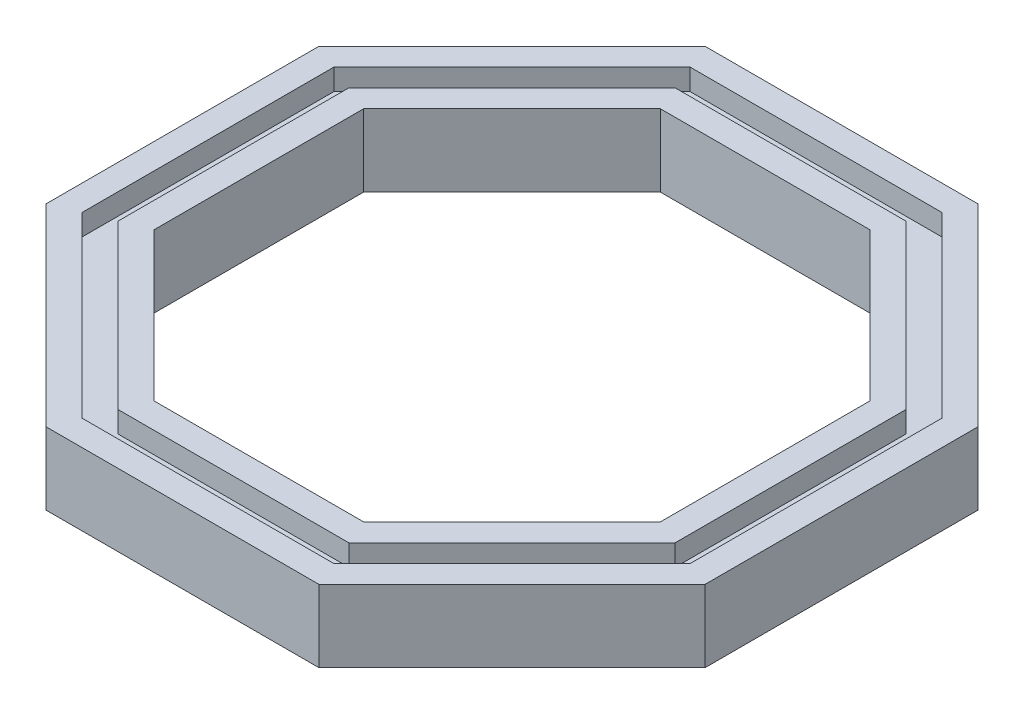
SolidWorks part; units mm, degrees
ref_plane "정면" through (0, 0, 0) normal (0, 0, 1) x (1, 0, 0)
ref_plane "윗면" through (0, 0, 0) normal (0, 1, 0) x (1, 0, 0)
ref_plane "우측면" through (0, 0, 0) normal (1, 0, 0) x (0, 0, -1)
sketch "스케치1" plane through (0, 0, 0) normal (0, 1, 0) x (1, 0, 0)
  line L0 (-55, 0) -> (55, 0) construction
  line L1 (5.9316, -14.3201) -> (14.3201, -5.9316)
  line L2 (14.3201, -5.9316) -> (14.3201, 5.9316)
  line L3 (14.3201, 5.9316) -> (5.9316, 14.3201)
  line L4 (5.9316, 14.3201) -> (-5.9316, 14.3201)
  line L5 (-5.9316, 14.3201) -> (-14.3201, 5.9316)
  line L6 (-14.3201, 5.9316) -> (-14.3201, -5.9316)
  line L7 (-14.3201, -5.9316) -> (-5.9316, -14.3201)
  line L8 (-5.9316, -14.3201) -> (5.9316, -14.3201)
  line L9 (6.4286, -15.5201) -> (15.5201, -6.4286)
  line L10 (15.5201, -6.4286) -> (15.5201, 6.4286)
  line L11 (15.5201, 6.4286) -> (6.4286, 15.5201)
  line L12 (6.4286, 15.5201) -> (-6.4286, 15.5201)
  line L13 (-6.4286, 15.5201) -> (-15.5201, 6.4286)
  line L14 (-15.5201, 6.4286) -> (-15.5201, -6.4286)
  line L15 (-15.5201, -6.4286) -> (-6.4286, -15.5201)
  line L16 (-6.4286, -15.5201) -> (6.4286, -15.5201)
  line L17 (5.4345, -13.1201) -> (13.1201, -5.4345)
  line L18 (13.1201, -5.4345) -> (13.1201, 5.4345)
  line L19 (13.1201, 5.4345) -> (5.4345, 13.1201)
  line L20 (5.4345, 13.1201) -> (-5.4345, 13.1201)
  line L21 (-5.4345, 13.1201) -> (-13.1201, 5.4345)
  line L22 (-13.1201, 5.4345) -> (-13.1201, -5.4345)
  line L23 (-13.1201, -5.4345) -> (-5.4345, -13.1201)
  line L24 (-5.4345, -13.1201) -> (5.4345, -13.1201)
  line L25 (4.9375, -11.9201) -> (11.9201, -4.9375)
  line L26 (11.9201, -4.9375) -> (11.9201, 4.9375)
  line L27 (11.9201, 4.9375) -> (4.9375, 11.9201)
  line L28 (4.9375, 11.9201) -> (-4.9375, 11.9201)
  line L29 (-4.9375, 11.9201) -> (-11.9201, 4.9375)
  line L30 (-11.9201, 4.9375) -> (-11.9201, -4.9375)
  line L31 (-11.9201, -4.9375) -> (-4.9375, -11.9201)
  line L32 (-4.9375, -11.9201) -> (4.9375, -11.9201)
  circle A0 centre (0, 0) radius 15.5 construction
  dimension "D1" = 31
  dimension "D2" = 1.2
  dimension "D3" = 1.2
  dimension "D4" = 1.2
extrude "보스-돌출1" add sketch "스케치1" along normal blind 3.4 contours L23 L24 L17 L18 L19 L20 L21 L22 L32 L31 L30 L29 L28 L27 L26 L25 | L7 L8 L1 L2 L3 L4 L5 L6 L24 L23 L22 L21 L20 L19 L18 L17 | L15 L16 L9 L10 L11 L12 L13 L14 L8 L7 L6 L5 L4 L3 L2 L1
sketch "스케치3" plane through (0, 3.4, 0) normal (0, 1, 0) x (1, 0, 0)
  line L17 (-13.1201, -5.4345) -> (-5.4345, -13.1201)
  line L18 (-5.4345, -13.1201) -> (5.4345, -13.1201)
  line L19 (5.4345, -13.1201) -> (13.1201, -5.4345)
  line L20 (13.1201, -5.4345) -> (13.1201, 5.4345)
  line L21 (13.1201, 5.4345) -> (5.4345, 13.1201)
  line L22 (5.4345, 13.1201) -> (-5.4345, 13.1201)
  line L23 (-5.4345, 13.1201) -> (-13.1201, 5.4345)
  line L24 (-14.3201, -5.9316) -> (-5.9316, -14.3201)
  line L25 (-5.9316, -14.3201) -> (5.9316, -14.3201)
  line L26 (5.9316, -14.3201) -> (14.3201, -5.9316)
  line L27 (14.3201, -5.9316) -> (14.3201, 5.9316)
  line L28 (14.3201, 5.9316) -> (5.9316, 14.3201)
  line L29 (5.9316, 14.3201) -> (-5.9316, 14.3201)
  line L30 (-5.9316, 14.3201) -> (-14.3201, 5.9316)
  line L31 (-14.3201, 5.9316) -> (-14.3201, -5.9316)
  line L32 (-14.3201, -5.9316) -> (-5.9316, -14.3201)
  line L33 (-5.9316, -14.3201) -> (5.9316, -14.3201)
  line L34 (5.9316, -14.3201) -> (14.3201, -5.9316)
  line L35 (14.3201, -5.9316) -> (14.3201, 5.9316)
  line L36 (14.3201, 5.9316) -> (5.9316, 14.3201)
  line L37 (5.9316, 14.3201) -> (-5.9316, 14.3201)
  line L38 (-5.9316, 14.3201) -> (-14.3201, 5.9316)
  line L39 (-14.3201, 5.9316) -> (-14.3201, -5.9316)
  line L40 (-13.1201, 5.4345) -> (-13.1201, -5.4345)
  dimension "D1" = 1.2
  dimension "D2" = 1.2
extrude "컷-돌출1" cut sketch "스케치3" against normal blind 1
ref_plane "평면1" through (0, 1.7, 0) normal (0, 1, 0) x (1, 0, 0)
mirror "대칭 복사1" about plane through (0, 1.7, 0) normal (0, 1, 0) of "컷-돌출1"
